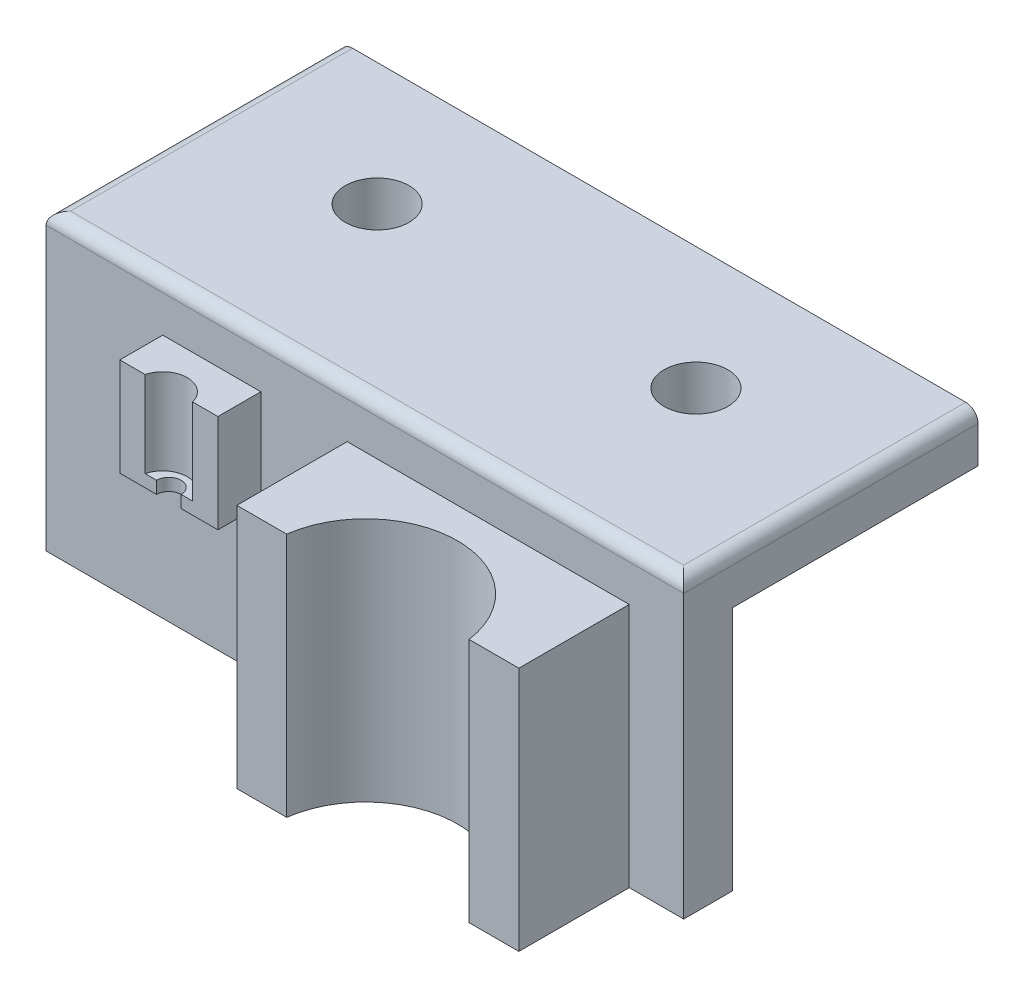
SolidWorks part; units mm, degrees
ref_plane "前视基准面" through (0, 0, 0) normal (0, 0, 1) x (1, 0, 0)
ref_plane "上视基准面" through (0, 0, 0) normal (0, 1, 0) x (1, 0, 0)
ref_plane "右视基准面" through (0, 0, 0) normal (1, 0, 0) x (0, 0, -1)
sketch "草图1" plane through (0, 0, 0) normal (0, 0, 1) x (1, 0, 0)
  line L1 (-20.0535, 11.3369) -> (19.9465, 11.3369)
  line L2 (-20.0535, 11.3369) -> (-20.0535, -28.6631)
  line L3 (-20.0535, -28.6631) -> (19.9465, -28.6631)
  line L4 (19.9465, 11.3369) -> (19.9465, -28.6631)
  dimension "D1" = 40
  dimension "D2" = 40
extrude "凸台-拉伸1" add sketch "草图1" along normal blind 4
sketch "草图2" plane through (0, 11.3369, 0) normal (0, 1, 0) x (1, 0, 0)
  line L4 (19.9465, 0) -> (-20.0535, 0)
  line L5 (-20.0535, 0) -> (-20.0535, -4)
  line L6 (-20.0535, -4) -> (19.9465, -4)
  line L7 (19.9465, -4) -> (19.9465, 0)
  line L8 (19.9465, 0) -> (-20.0535, 0)
  line L9 (-20.0535, 0) -> (-20.0535, -4)
  line L10 (-20.0535, -4) -> (19.9465, -4)
  line L11 (19.9465, -4) -> (19.9465, 0)
  dimension "D1" = 0
extrude "凸台-拉伸2" add sketch "草图2" along normal blind 4
sketch "草图3" plane through (0, 0, 0) normal (0, 0, -1) x (-1, 0, 0)
  line L0 (-19.9465, 11.3369) -> (20.0535, 11.3369)
  line L1 (-19.9465, -28.6631) -> (-19.9465, 15.3369) construction
  line L2 (20.0535, 15.3369) -> (20.0535, -28.6631) construction
  line L3 (-19.9465, 15.3369) -> (20.0535, 15.3369) construction
  line L4 (-19.9465, 11.3369) -> (-19.9465, 15.3369)
  line L5 (-19.9465, 15.3369) -> (20.0535, 15.3369)
  line L6 (20.0535, 15.3369) -> (20.0535, 11.3369)
  dimension "D1" = 4
extrude "凸台-拉伸3" add sketch "草图3" along normal blind 20
sketch "草图4" plane through (0, 0, 4) normal (0, 0, 1) x (1, 0, 0)
  line L0 (-0.0535, 15.3369) -> (-0.0535, -28.6631)
  line L1 (-20.0535, 15.3369) -> (19.9465, 15.3369) construction
  line L2 (-20.0535, -28.6631) -> (19.9465, -28.6631) construction
  line L3 (-14.5346, 15.3369) -> (-6.5346, 15.3369)
  line L4 (-14.5346, 15.3369) -> (-14.5346, 3.3369)
  line L5 (-6.5346, 15.3369) -> (-6.5346, 3.3369)
  line L6 (-14.5346, 3.3369) -> (-6.5346, 3.3369)
  line M8 (19.9465, 15.3369) -> (-20.0535, 15.3369)
  dimension "D3" = 12
extrude "凸台-拉伸4" add sketch "草图4" along normal blind 4 contours L4 L6 L5 M8
sketch "草图6" plane through (0, 15.3369, 0) normal (0, 1, 0) x (1, 0, 0)
  line L0 (-6.5346, -8) -> (-14.5346, -8) construction
  line L1 (-8.5346, -8) -> (-12.5346, -8)
  arc A0 (-8.5346, -8) -> (-12.5346, -8) centre (-10.5346, -8) ccw
  dimension "D1" = 4
extrude "切除-拉伸1" cut sketch "草图6" against normal blind 11
sketch "草图8" plane through (-20.0535, 0, 0) normal (-1, 0, 0) x (0, 0, 1)
  line L6 (4, 15.3369) -> (-20, 15.3369)
  line L7 (-20, 15.3369) -> (-20, 11.3369)
  line L8 (-20, 11.3369) -> (0, 11.3369)
  line L9 (0, 11.3369) -> (0, -28.6631)
  line L10 (0, -28.6631) -> (4, -28.6631)
  line L11 (4, -28.6631) -> (4, 15.3369)
  line L12 (4, 15.3369) -> (-20, 15.3369)
  line L13 (-20, 15.3369) -> (-20, 11.3369)
  line L14 (-20, 11.3369) -> (0, 11.3369)
  line L15 (0, 11.3369) -> (0, -28.6631)
  line L16 (0, -28.6631) -> (4, -28.6631)
  line L17 (4, -28.6631) -> (4, 15.3369)
  dimension "D1" = 0
extrude "凸台-拉伸5" add sketch "草图8" along normal blind 4
sketch "草图9" plane through (19.9465, 0, 0) normal (1, 0, 0) x (0, 0, -1)
  line L6 (0, -28.6631) -> (0, 11.3369)
  line L7 (0, 11.3369) -> (20, 11.3369)
  line L8 (20, 11.3369) -> (20, 15.3369)
  line L9 (20, 15.3369) -> (-4, 15.3369)
  line L10 (-4, 15.3369) -> (-4, -28.6631)
  line L11 (-4, -28.6631) -> (0, -28.6631)
  line L12 (0, -28.6631) -> (0, 11.3369)
  line L13 (0, 11.3369) -> (20, 11.3369)
  line L14 (20, 11.3369) -> (20, 15.3369)
  line L15 (20, 15.3369) -> (-4, 15.3369)
  line L16 (-4, 15.3369) -> (-4, -28.6631)
  line L17 (-4, -28.6631) -> (0, -28.6631)
  dimension "D1" = 0
extrude "凸台-拉伸6" add sketch "草图9" along normal blind 4
sketch "草图10" plane through (0, 0, 4) normal (0, 0, 1) x (1, 0, 0)
  line L0 (0.5074, 15.3369) -> (23.5074, 15.3369)
  line L1 (-6.5346, 15.3369) -> (23.9465, 15.3369) construction
  line L2 (0.5074, 15.3369) -> (0.5074, -8.9562)
  line L3 (23.5074, 15.3369) -> (23.5074, -8.9562)
  line L5 (0.5074, -8.9562) -> (23.5074, -8.9562)
sketch "草图11" plane through (23.9465, 0, 0) normal (1, 0, 0) x (0, 0, -1)
  line L6 (-4, -28.6631) -> (0, -28.6631)
  line L7 (0, -28.6631) -> (0, 11.3369)
  line L8 (0, 11.3369) -> (20, 11.3369)
  line L9 (20, 11.3369) -> (20, 15.3369)
  line L10 (20, 15.3369) -> (-4, 15.3369)
  line L11 (-4, 15.3369) -> (-4, -28.6631)
  line L12 (-4, -28.6631) -> (0, -28.6631)
  line L13 (0, -28.6631) -> (0, 11.3369)
  line L14 (0, 11.3369) -> (20, 11.3369)
  line L15 (20, 11.3369) -> (20, 15.3369)
  line L16 (20, 15.3369) -> (-4, 15.3369)
  line L17 (-4, 15.3369) -> (-4, -28.6631)
  dimension "D1" = 0
extrude "凸台-拉伸7" add sketch "草图11" along normal blind 4
extrude "凸台-拉伸8" add sketch "草图10" along normal blind 10
sketch "草图12" plane through (0, -8.9562, 0) normal (0, -1, 0) x (1, 0, 0)
  line L0 (0.5074, 14) -> (23.5074, 14) construction
  line L1 (4.5074, 14) -> (19.5074, 14)
  arc A0 (4.5074, 14) -> (19.5074, 14) centre (12.0074, 14) ccw
  dimension "D1" = 15
extrude "切除-拉伸3" cut sketch "草图12" against normal through all
sketch "草图14" plane through (0, 15.3369, 0) normal (0, 1, 0) x (1, 0, 0)
  line L0 (-6.5346, -7.5) -> (-14.5346, -7.5)
  line L1 (-6.5346, -8) -> (-6.5346, -4) construction
  line L2 (-14.5346, -8) -> (-14.5346, -4) construction
  line L3 (-12.5346, -8) -> (-14.5346, -8) construction
  line L4 (-6.5346, -7.5) -> (-6.5346, -8)
  line L5 (-6.5346, -8) -> (-14.5346, -8)
  line L6 (-14.5346, -8) -> (-14.5346, -7.5)
  dimension "D1" = 0.5
extrude "切除-拉伸4" cut sketch "草图14" against normal through all
sketch "草图15" plane through (0, 15.3369, 0) normal (0, 1, 0) x (1, 0, 0)
  line L0 (23.5074, -13) -> (0.5074, -13)
  line L1 (23.5074, -14) -> (23.5074, -4) construction
  line L2 (0.5074, -14) -> (0.5074, -4) construction
  line L3 (4.5074, -14) -> (0.5074, -14) construction
  line L4 (23.5074, -13) -> (23.5074, -14)
  line L5 (23.5074, -14) -> (0.5074, -14)
  line L6 (0.5074, -14) -> (0.5074, -13)
  dimension "D1" = 1
extrude "切除-拉伸5" cut sketch "草图15" against normal through all
sketch "草图16" plane through (0, 15.3369, 0) normal (0, 1, 0) x (1, 0, 0)
  circle A0 centre (-11.0535, 10) radius 2.6
  circle A1 centre (14.9465, 10) radius 2.6
  dimension "D4" = 5.2
  dimension "D5" = 5.2
extrude "切除-拉伸6" cut sketch "草图16" against normal blind 7
sketch "草图17" plane through (0, -28.6631, 0) normal (0, -1, 0) x (1, 0, 0)
  line L4 (-24.0535, 0) -> (27.9465, 0)
  line L5 (27.9465, 0) -> (27.9465, 4)
  line L6 (27.9465, 4) -> (-24.0535, 4)
  line L7 (-24.0535, 4) -> (-24.0535, 0)
  line L8 (-24.0535, 0) -> (27.9465, 0)
  line L9 (27.9465, 0) -> (27.9465, 4)
  line L10 (27.9465, 4) -> (-24.0535, 4)
  line L11 (-24.0535, 4) -> (-24.0535, 0)
  dimension "D1" = 0
extrude "切除-拉伸7" cut sketch "草图17" against normal blind 20
sketch "草图19" plane through (0, -8.9562, 0) normal (0, -1, 0) x (1, 0, 0)
  line L5 (23.5074, 4) -> (23.5074, 13)
  line L6 (23.5074, 13) -> (19.4404, 13)
  line L7 (4.5743, 13) -> (0.5074, 13)
  line L8 (0.5074, 13) -> (0.5074, 4)
  line L9 (0.5074, 4) -> (23.5074, 4)
  line L10 (23.5074, 4) -> (23.5074, 13)
  line L11 (23.5074, 13) -> (19.4404, 13)
  line L12 (4.5743, 13) -> (0.5074, 13)
  line L13 (0.5074, 13) -> (0.5074, 4)
  line L14 (0.5074, 4) -> (23.5074, 4)
  arc A1 (4.5743, 13) -> (19.4404, 13) centre (12.0074, 14) ccw
  arc A2 (4.5743, 13) -> (19.4404, 13) centre (12.0074, 14) ccw
  dimension "D1" = 0
extrude "切除-拉伸8" cut sketch "草图19" against normal blind 0.29
sketch "草图20" plane through (0, 3.3369, 0) normal (0, -1, 0) x (-1, 0, 0)
  line L0 (6.5346, -7.5) -> (14.5346, -7.5) construction
  circle A0 centre (10.5346, -7.5) radius 1
  dimension "D1" = 2
extrude "切除-拉伸9" cut sketch "草图20" against normal blind 11
sketch "草图21" plane through (0, 15.3369, 0) normal (0, 1, 0) x (1, 0, 0)
  line L0 (27.9465, -4) -> (-24.0535, -4)
extrude "切除-拉伸10" cut sketch "草图21" against normal blind 4 and the other way through all
fillet "圆角1" radius 1 3 edges at (-24.0535, 15.3369, -8) (1.9465, 15.3369, 4) (27.9465, 15.3369, -8)
